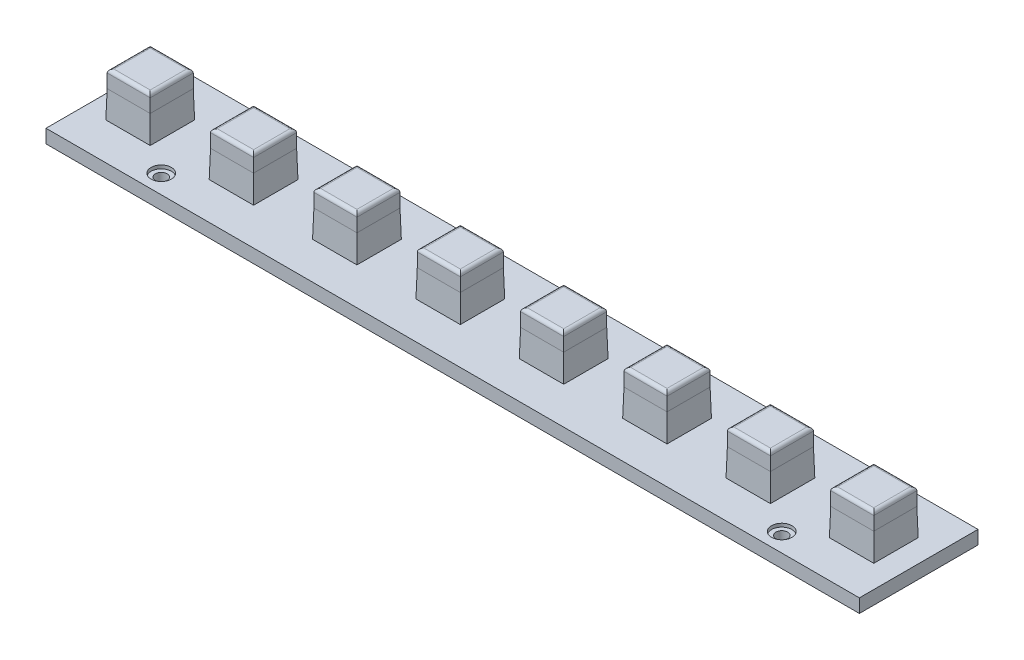
SolidWorks part; units mm, degrees
ref_plane "Front Plane" through (0, 0, 0) normal (0, 0, 1) x (1, 0, 0)
ref_plane "Top Plane" through (0, 0, 0) normal (0, 1, 0) x (1, 0, 0)
ref_plane "Right Plane" through (0, 0, 0) normal (1, 0, 0) x (0, 0, -1)
sketch "Sketch1" plane through (0, 0, 0) normal (0, 1, 0) x (1, 0, 0)
  line L0 (0, 17.5) -> (13.25, 17.5) construction
  line L1 (0, 0) -> (240, 0)
  line L2 (0, 0) -> (0, 35)
  line L3 (0, 35) -> (240, 35)
  line L4 (240, 0) -> (240, 35)
  line L5 (0, 0) -> (240, 35) construction
  line L6 (0, 35) -> (240, 0) construction
  line L7 (13.25, 17.5) -> (43.75, 17.5) construction
  line L8 (43.75, 17.5) -> (74.25, 17.5) construction
  line L9 (74.25, 17.5) -> (104.75, 17.5) construction
  line L10 (104.75, 17.5) -> (135.25, 17.5) construction
  line L11 (135.25, 17.5) -> (165.75, 17.5) construction
  line L12 (165.75, 17.5) -> (196.25, 17.5) construction
  line L14 (6.9, 23.85) -> (19.6, 23.85)
  line L15 (6.9, 23.85) -> (6.9, 11.15)
  line L16 (6.9, 11.15) -> (19.6, 11.15)
  line L17 (19.6, 23.85) -> (19.6, 11.15)
  line L18 (6.9, 23.85) -> (19.6, 11.15) construction
  line L19 (6.9, 11.15) -> (19.6, 23.85) construction
  line L23 (196.25, 17.5) -> (226.75, 17.5) construction
  line L24 (37.4, 23.85) -> (50.1, 23.85)
  line L25 (37.4, 23.85) -> (37.4, 11.15)
  line L26 (37.4, 11.15) -> (50.1, 11.15)
  line L27 (50.1, 23.85) -> (50.1, 11.15)
  line L28 (37.4, 23.85) -> (50.1, 11.15) construction
  line L29 (37.4, 11.15) -> (50.1, 23.85) construction
  line L30 (67.9, 23.85) -> (80.6, 23.85)
  line L31 (67.9, 23.85) -> (67.9, 11.15)
  line L32 (67.9, 11.15) -> (80.6, 11.15)
  line L33 (80.6, 23.85) -> (80.6, 11.15)
  line L34 (67.9, 23.85) -> (80.6, 11.15) construction
  line L35 (67.9, 11.15) -> (80.6, 23.85) construction
  line L36 (98.4, 23.85) -> (111.1, 23.85)
  line L37 (98.4, 23.85) -> (98.4, 11.15)
  line L38 (98.4, 11.15) -> (111.1, 11.15)
  line L39 (111.1, 23.85) -> (111.1, 11.15)
  line L40 (98.4, 23.85) -> (111.1, 11.15) construction
  line L41 (98.4, 11.15) -> (111.1, 23.85) construction
  line L42 (128.9, 23.85) -> (141.6, 23.85)
  line L43 (128.9, 23.85) -> (128.9, 11.15)
  line L44 (128.9, 11.15) -> (141.6, 11.15)
  line L45 (141.6, 23.85) -> (141.6, 11.15)
  line L46 (128.9, 23.85) -> (141.6, 11.15) construction
  line L47 (128.9, 11.15) -> (141.6, 23.85) construction
  line L48 (159.4, 23.85) -> (172.1, 23.85)
  line L49 (159.4, 23.85) -> (159.4, 11.15)
  line L50 (159.4, 11.15) -> (172.1, 11.15)
  line L51 (172.1, 23.85) -> (172.1, 11.15)
  line L52 (159.4, 23.85) -> (172.1, 11.15) construction
  line L53 (159.4, 11.15) -> (172.1, 23.85) construction
  line L54 (226.75, 17.5) -> (240, 17.5) construction
  line L56 (189.9, 23.85) -> (202.6, 23.85)
  line L57 (189.9, 23.85) -> (189.9, 11.15)
  line L58 (189.9, 11.15) -> (202.6, 11.15)
  line L59 (202.6, 23.85) -> (202.6, 11.15)
  line L60 (189.9, 23.85) -> (202.6, 11.15) construction
  line L61 (189.9, 11.15) -> (202.6, 23.85) construction
  line L62 (220.4, 23.85) -> (233.1, 23.85)
  line L63 (220.4, 23.85) -> (220.4, 11.15)
  line L64 (220.4, 11.15) -> (233.1, 11.15)
  line L65 (233.1, 23.85) -> (233.1, 11.15)
  line L66 (220.4, 23.85) -> (233.1, 11.15) construction
  line L67 (220.4, 11.15) -> (233.1, 23.85) construction
  point P4 (120, 17.5)
  point P18 (13.25, 17.5)
  point P24 (43.75, 17.5)
  point P28 (74.25, 17.5)
  point P33 (104.75, 17.5)
  point P38 (135.25, 17.5)
  point P43 (165.75, 17.5)
  point P55 (196.25, 17.5)
  point P56 (226.75, 17.5)
  dimension "D1" = 12.7
  dimension "D2" = 30.5
  dimension "D3" = 240
  dimension "D4" = 35
extrude "Boss-Extrude1" add sketch "Sketch1" along normal blind 4
sketch "Sketch2" plane through (0, 4, 0) normal (0, 1, 0) x (1, 0, 0)
  line L0 (189.9, 11.15) -> (202.6, 11.15) construction
  line L1 (6.9, 23.85) -> (19.6, 23.85)
  line L2 (6.9, 23.85) -> (6.9, 11.15)
  line L3 (6.9, 11.15) -> (19.6, 11.15)
  line L4 (19.6, 23.85) -> (19.6, 11.15)
  line L5 (6.9, 23.85) -> (19.6, 11.15) construction
  line L6 (6.9, 11.15) -> (19.6, 23.85) construction
  line L7 (37.4, 23.85) -> (50.1, 23.85)
  line L8 (37.4, 23.85) -> (37.4, 11.15)
  line L9 (37.4, 11.15) -> (50.1, 11.15)
  line L10 (50.1, 23.85) -> (50.1, 11.15)
  line L11 (37.4, 23.85) -> (50.1, 11.15) construction
  line L12 (37.4, 11.15) -> (50.1, 23.85) construction
  line L13 (67.9, 23.85) -> (80.6, 23.85)
  line L14 (67.9, 23.85) -> (67.9, 11.15)
  line L15 (67.9, 11.15) -> (80.6, 11.15)
  line L16 (80.6, 23.85) -> (80.6, 11.15)
  line L17 (67.9, 23.85) -> (80.6, 11.15) construction
  line L18 (67.9, 11.15) -> (80.6, 23.85) construction
  line L19 (98.4, 23.85) -> (111.1, 23.85)
  line L20 (98.4, 23.85) -> (98.4, 11.15)
  line L21 (98.4, 11.15) -> (111.1, 11.15)
  line L22 (111.1, 23.85) -> (111.1, 11.15)
  line L23 (98.4, 23.85) -> (111.1, 11.15) construction
  line L24 (98.4, 11.15) -> (111.1, 23.85) construction
  line L25 (128.9, 23.85) -> (141.6, 23.85)
  line L26 (128.9, 23.85) -> (128.9, 11.15)
  line L27 (128.9, 11.15) -> (141.6, 11.15)
  line L28 (141.6, 23.85) -> (141.6, 11.15)
  line L29 (128.9, 23.85) -> (141.6, 11.15) construction
  line L30 (128.9, 11.15) -> (141.6, 23.85) construction
  line L31 (159.4, 23.85) -> (172.1, 23.85)
  line L32 (159.4, 23.85) -> (159.4, 11.15)
  line L33 (159.4, 11.15) -> (172.1, 11.15)
  line L34 (172.1, 23.85) -> (172.1, 11.15)
  line L35 (159.4, 23.85) -> (172.1, 11.15) construction
  line L36 (159.4, 11.15) -> (172.1, 23.85) construction
  line L37 (189.9, 23.85) -> (202.6, 23.85)
  line L38 (189.9, 23.85) -> (189.9, 11.15)
  line L39 (189.9, 11.15) -> (202.6, 11.15)
  line L40 (202.6, 23.85) -> (202.6, 11.15)
  line L41 (189.9, 23.85) -> (202.6, 11.15) construction
  line L42 (189.9, 11.15) -> (202.6, 23.85) construction
  line L43 (220.4, 23.85) -> (233.1, 23.85)
  line L44 (220.4, 23.85) -> (220.4, 11.15)
  line L45 (220.4, 11.15) -> (233.1, 11.15)
  line L46 (233.1, 23.85) -> (233.1, 11.15)
  line L47 (220.4, 23.85) -> (233.1, 11.15) construction
  line L48 (220.4, 11.15) -> (233.1, 23.85) construction
  line L49 (202.6, 11.15) -> (202.6, 23.85) construction
  line L50 (19.6, 11.15) -> (19.6, 23.85) construction
  line L51 (6.9, 11.15) -> (19.6, 11.15) construction
  point P4 (13.25, 17.5)
  point P9 (43.75, 17.5)
  point P14 (74.25, 17.5)
  point P19 (104.75, 17.5)
  point P24 (135.25, 17.5)
  point P29 (165.75, 17.5)
  point P34 (196.25, 17.5)
  point P39 (226.75, 17.5)
extrude "Boss-Extrude2" add sketch "Sketch2" along normal blind 13 and the other way up to surface (4 mm away) other way up to face at (120, 0, -17.5)
chamfer "Chamfer1" distance 0.2 distance2 8 32 edges at (19.6, 4, -17.5) (13.25, 4, -23.85) (6.9, 4, -17.5) (13.25, 4, -11.15) (37.4, 4, -17.5) (43.75, 4, -11.15) (50.1, 4, -17.5) (43.75, 4, -23.85) (80.6, 4, -17.5) (74.25, 4, -11.15) (67.9, 4, -17.5) (74.25, 4, -23.85) (111.1, 4, -17.5) (104.75, 4, -11.15) (98.4, 4, -17.5) (104.75, 4, -23.85) (141.6, 4, -17.5) (135.25, 4, -11.15) (128.9, 4, -17.5) (135.25, 4, -23.85) (172.1, 4, -17.5) (165.75, 4, -11.15) (159.4, 4, -17.5) (165.75, 4, -23.85) (202.6, 4, -17.5) (196.25, 4, -11.15) (189.9, 4, -17.5) (196.25, 4, -23.85) (233.1, 4, -17.5) (226.75, 4, -11.15) (220.4, 4, -17.5) (226.75, 4, -23.85)
sketch "Sketch3" plane through (0, 4, 0) normal (0, 1, 0) x (1, 0, 0)
  line L0 (19.6, 17.5) -> (37.4, 17.5) construction
  line L1 (19.6, 11.15) -> (19.6, 23.85) construction
  line L2 (37.4, 23.85) -> (37.4, 11.15) construction
  line L3 (37.4, 17.5) -> (202.8, 17.5) construction
  line L4 (202.8, 24.05) -> (202.8, 10.95) construction
  line L5 (202.8, 17.5) -> (220.4, 17.5) construction
  line L6 (220.4, 23.85) -> (220.4, 11.15) construction
  line L7 (28.5, 17.5) -> (28.5, 5.5) construction
  line L8 (28.5, 5.5) -> (211.6, 5.5) construction
  line L9 (211.6, 5.5) -> (211.6, 17.5) construction
  line L10 (211.6, 17.5) -> (211.6, 29.5) construction
  line L11 (211.6, 29.5) -> (28.5, 29.5) construction
  line L12 (28.5, 29.5) -> (28.5, 17.5) construction
  circle A0 centre (28.5, 5.5) radius 1.725
  circle A1 centre (28.5, 29.5) radius 1.725
  circle A2 centre (211.6, 29.5) radius 1.725
  circle A3 centre (211.6, 5.5) radius 1.725
  dimension "D1" = 3.45
  dimension "D2" = 24
extrude "Cut-Extrude1" cut sketch "Sketch3" against normal through all
sketch "Sketch4" plane through (0, 4, 0) normal (0, 1, 0) x (1, 0, 0)
  circle A0 centre (28.5, 29.5) radius 3
  circle A1 centre (28.5, 5.5) radius 3
  circle A2 centre (211.6, 5.5) radius 3
  circle A3 centre (211.6, 29.5) radius 3
  dimension "D1" = 6
extrude "Cut-Extrude2" cut sketch "Sketch4" against normal blind 1
fillet "Fillet1" radius 1 32 edges at (226.75, 17, -23.85) (233.1, 17, -17.5) (226.75, 17, -11.15) (220.4, 17, -17.5) (196.25, 17, -23.85) (202.6, 17, -17.5) (196.25, 17, -11.15) (189.9, 17, -17.5) (165.75, 17, -23.85) (172.1, 17, -17.5) (165.75, 17, -11.15) (159.4, 17, -17.5) (135.25, 17, -23.85) (141.6, 17, -17.5) (135.25, 17, -11.15) (128.9, 17, -17.5) (104.75, 17, -23.85) (111.1, 17, -17.5) (104.75, 17, -11.15) (98.4, 17, -17.5) (74.25, 17, -23.85) (80.6, 17, -17.5) (74.25, 17, -11.15) (67.9, 17, -17.5) (43.75, 17, -23.85) (50.1, 17, -17.5) (43.75, 17, -11.15) (37.4, 17, -17.5) (13.25, 17, -23.85) (19.6, 17, -17.5) (13.25, 17, -11.15) (6.9, 17, -17.5)
